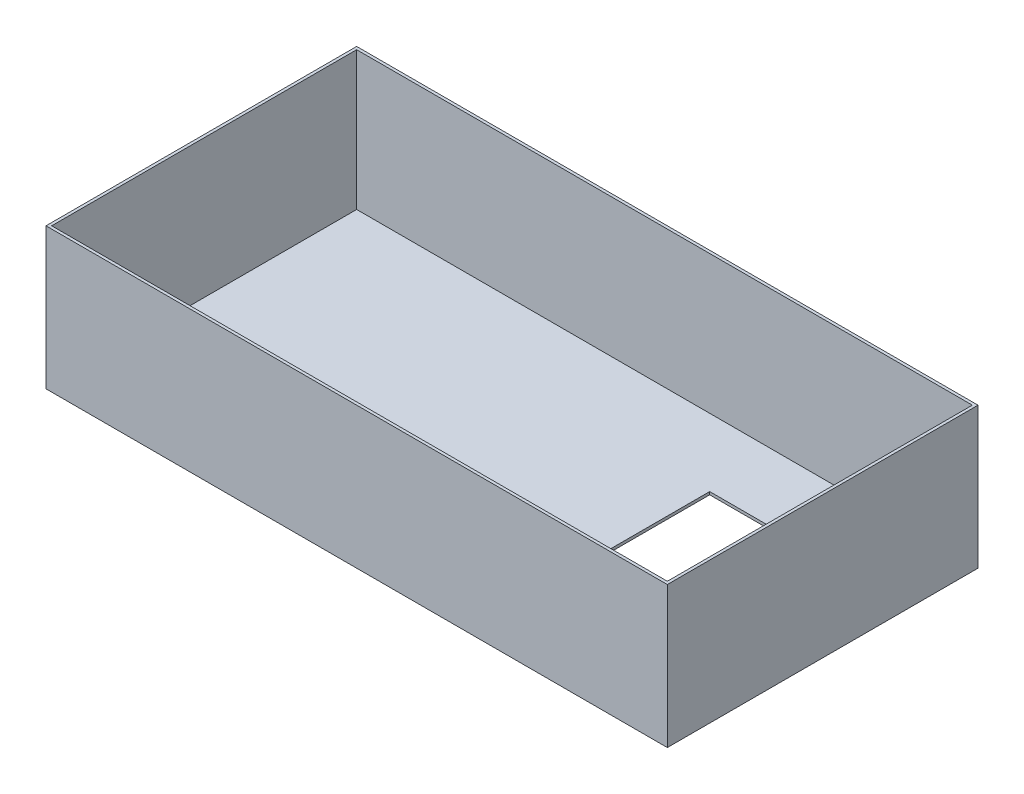
SolidWorks part; units mm, degrees
ref_plane "Front Plane" through (0, 0, 0) normal (0, 0, 1) x (1, 0, 0)
ref_plane "Top Plane" through (0, 0, 0) normal (0, 1, 0) x (1, 0, 0)
ref_plane "Right Plane" through (0, 0, 0) normal (1, 0, 0) x (0, 0, -1)
sketch "Sketch1" plane through (0, 0, 0) normal (0, 1, 0) x (1, 0, 0)
  line L1 (0, 0) -> (-2200, 0)
  line L2 (0, 0) -> (0, 1100)
  line L3 (0, 1100) -> (-2200, 1100)
  line L4 (-2200, 0) -> (-2200, 1100)
  dimension "D1" = 2200
  dimension "D2" = 1100
extrude "Extrude1" add sketch "Sketch1" along normal blind 500
shell "Shell1" thickness 10
sketch "Sketch2" plane through (0, 0, 0) normal (0, -1, 0) x (1, 0, 0)
  line L0 (-2200, 0) -> (0, 0) construction
  line L1 (-100, -250) -> (-700, -250)
  line L2 (-100, -250) -> (-100, -850)
  line L3 (-100, -850) -> (-700, -850)
  line L4 (-700, -250) -> (-700, -850)
  line L5 (0, 0) -> (0, -1100) construction
  dimension "D1" = 600
  dimension "D2" = 600
  dimension "D3" = 250
  dimension "D4" = 100
extrude "Cut-Extrude1" cut sketch "Sketch2" against normal blind 400
